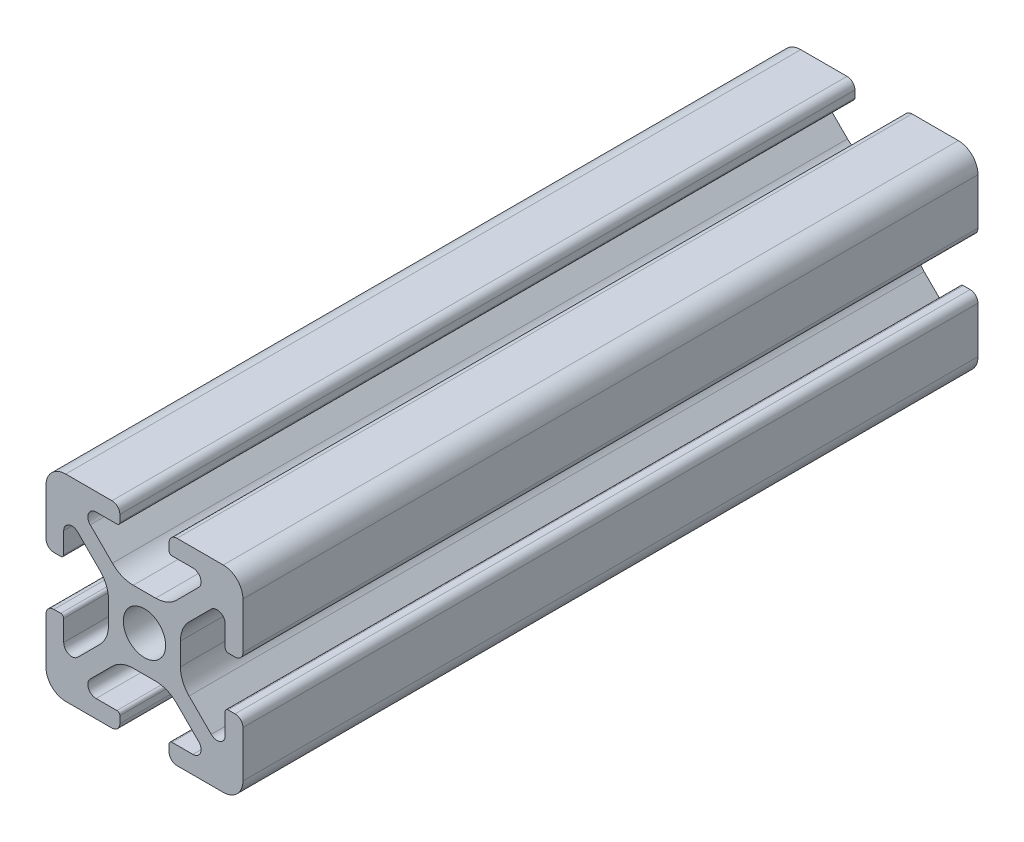
SolidWorks part; units mm, degrees
ref_plane "Front" through (0, 0, 0) normal (0, 0, 1) x (1, 0, 0)
ref_plane "Top" through (0, 0, 0) normal (0, 1, 0) x (1, 0, 0)
ref_plane "Right" through (0, 0, 0) normal (1, 0, 0) x (0, 0, -1)
sketch "Support-Front" plane through (0, 0, 0) normal (0, 0, 1) x (1, 0, 0)
  line L0 (10, 0) -> (-10, 0) construction
  line L1 (-10, -10) -> (10, -10)
  line L2 (-10, -10) -> (-10, 10)
  line L3 (-10, 10) -> (10, 10)
  line L4 (10, -10) -> (10, 10)
  line L5 (0, 10) -> (0, -10) construction
  dimension "Height-Profile" = 20
  dimension "Width-Profile" = 20
sketch "Support-Right-Length" plane through (0, 0, 0) normal (1, 0, 0) x (0, 0, -1)
  line L0 (0, -10) -> (0, 10) construction
  line L1 (-25, 10) -> (25, 10)
  line L2 (-25, 10) -> (-25, -10)
  line L3 (-25, -10) -> (25, -10)
  line L4 (25, 10) -> (25, -10)
  dimension "Length-Profile" = 50
sketch "Support-Profile" plane through (0, 0, 0) normal (0, 0, 1) x (1, 0, 0)
  line L8 (4.9176, -8.2) -> (2.8, -8.2)
  line L9 (2.5, -8.5) -> (2.5, -9.2)
  line L10 (3.3, -10) -> (8, -10)
  line L11 (10, -8) -> (10, -3.3)
  line L24 (9.2, -2.5) -> (8.5, -2.5)
  line L25 (8.2, -2.8) -> (8.2, -4.9176)
  line L26 (6.779, -5.5062) -> (4.5287, -3.2559)
  line L27 (3.65, -1.1346) -> (3.65, 1.1346)
  line L28 (4.5287, 3.2559) -> (6.779, 5.5062)
  line L29 (8.2, 4.9176) -> (8.2, 2.8)
  line L30 (8.5, 2.5) -> (9.2, 2.5)
  line L31 (10, 3.3) -> (10, 8)
  line L32 (8, 10) -> (3.3, 10)
  line L33 (2.5, 9.2) -> (2.5, 8.5)
  line L34 (2.8, 8.2) -> (4.9176, 8.2)
  line L35 (5.5062, 6.779) -> (3.2559, 4.5287)
  line L40 (1.1346, 3.65) -> (-1.1346, 3.65)
  line L41 (-3.2559, 4.5287) -> (-5.5062, 6.779)
  line L42 (-4.9176, 8.2) -> (-2.8, 8.2)
  line L43 (-2.5, 8.5) -> (-2.5, 9.2)
  line L44 (-3.3, 10) -> (-8, 10)
  line L45 (-10, 8) -> (-10, 3.3)
  line L46 (-9.2, 2.5) -> (-8.5, 2.5)
  line L47 (-8.2, 2.8) -> (-8.2, 4.9176)
  line L48 (-6.779, 5.5062) -> (-4.5287, 3.2559)
  line L49 (-3.65, 1.1346) -> (-3.65, -1.1346)
  line L50 (-4.5287, -3.2559) -> (-6.779, -5.5062)
  line L51 (-8.2, -4.9176) -> (-8.2, -2.8)
  line L52 (-8.5, -2.5) -> (-9.2, -2.5)
  line L53 (-10, -3.3) -> (-10, -8)
  line L54 (-8, -10) -> (-3.3, -10)
  line L55 (-2.5, -9.2) -> (-2.5, -8.5)
  line L56 (-2.8, -8.2) -> (-4.9176, -8.2)
  line L57 (-5.5062, -6.779) -> (-3.2559, -4.5287)
  line L58 (-1.1346, -3.65) -> (1.1346, -3.65)
  line L59 (3.2559, -4.5287) -> (5.5062, -6.779)
  circle A2 centre (0, 0) radius 2.15
  arc A3 (2.8, -8.2) -> (2.5, -8.5) centre (2.8, -8.5) ccw
  arc A5 (2.5, -9.2) -> (3.3, -10) centre (3.3, -9.2) ccw
  arc A24 (8, -10) -> (10, -8) centre (8, -8) ccw
  arc A25 (10, -3.3) -> (9.2, -2.5) centre (9.2, -3.3) ccw
  arc A26 (8.5, -2.5) -> (8.2, -2.8) centre (8.5, -2.8) ccw
  arc A27 (6.779, -5.5062) -> (8.2, -4.9176) centre (7.3676, -4.9176) ccw
  arc A28 (3.65, -1.1346) -> (4.5287, -3.2559) centre (6.65, -1.1346) ccw
  arc A29 (4.5287, 3.2559) -> (3.65, 1.1346) centre (6.65, 1.1346) ccw
  arc A30 (8.2, 4.9176) -> (6.779, 5.5062) centre (7.3676, 4.9176) ccw
  arc A31 (8.2, 2.8) -> (8.5, 2.5) centre (8.5, 2.8) ccw
  arc A32 (9.2, 2.5) -> (10, 3.3) centre (9.2, 3.3) ccw
  arc A33 (10, 8) -> (8, 10) centre (8, 8) ccw
  arc A34 (3.3, 10) -> (2.5, 9.2) centre (3.3, 9.2) ccw
  arc A35 (2.5, 8.5) -> (2.8, 8.2) centre (2.8, 8.5) ccw
  arc A38 (5.5062, 6.779) -> (4.9176, 8.2) centre (4.9176, 7.3676) ccw
  arc A39 (1.1346, 3.65) -> (3.2559, 4.5287) centre (1.1346, 6.65) ccw
  arc A44 (-3.2559, 4.5287) -> (-1.1346, 3.65) centre (-1.1346, 6.65) ccw
  arc A45 (-4.9176, 8.2) -> (-5.5062, 6.779) centre (-4.9176, 7.3676) ccw
  arc A46 (-2.8, 8.2) -> (-2.5, 8.5) centre (-2.8, 8.5) ccw
  arc A47 (-2.5, 9.2) -> (-3.3, 10) centre (-3.3, 9.2) ccw
  arc A48 (-8, 10) -> (-10, 8) centre (-8, 8) ccw
  arc A49 (-10, 3.3) -> (-9.2, 2.5) centre (-9.2, 3.3) ccw
  arc A50 (-8.5, 2.5) -> (-8.2, 2.8) centre (-8.5, 2.8) ccw
  arc A51 (-6.779, 5.5062) -> (-8.2, 4.9176) centre (-7.3676, 4.9176) ccw
  arc A52 (-3.65, 1.1346) -> (-4.5287, 3.2559) centre (-6.65, 1.1346) ccw
  arc A53 (-4.5287, -3.2559) -> (-3.65, -1.1346) centre (-6.65, -1.1346) ccw
  arc A54 (-8.2, -4.9176) -> (-6.779, -5.5062) centre (-7.3676, -4.9176) ccw
  arc A55 (-8.2, -2.8) -> (-8.5, -2.5) centre (-8.5, -2.8) ccw
  arc A56 (-9.2, -2.5) -> (-10, -3.3) centre (-9.2, -3.3) ccw
  arc A57 (-10, -8) -> (-8, -10) centre (-8, -8) ccw
  arc A58 (-3.3, -10) -> (-2.5, -9.2) centre (-3.3, -9.2) ccw
  arc A59 (-2.5, -8.5) -> (-2.8, -8.2) centre (-2.8, -8.5) ccw
  arc A60 (-5.5062, -6.779) -> (-4.9176, -8.2) centre (-4.9176, -7.3676) ccw
  arc A61 (-1.1346, -3.65) -> (-3.2559, -4.5287) centre (-1.1346, -6.65) ccw
  arc A62 (3.2559, -4.5287) -> (1.1346, -3.65) centre (1.1346, -6.65) ccw
  arc A63 (4.9176, -8.2) -> (5.5062, -6.779) centre (4.9176, -7.3676) ccw
ref_plane "Ref-Plane-1" through (0, 0, 25) normal (0, 0, 1) x (1, 0, 0)
ref_plane "Ref-Plane-2" through (0, 0, -25) normal (0, 0, 1) x (1, 0, 0)
sketch "Sketch4" plane through (0, 0, 25) normal (0, 0, 1) x (1, 0, 0)
  line L0 (-10, -10) -> (-10, 10) construction
  line L1 (-10, -10) -> (10, -10) construction
  line L2 (10, -10) -> (10, 10) construction
  line L3 (-10, 10) -> (10, 10) construction
  line L4 (-10, -10) -> (-10, 10)
  line L5 (-10, -10) -> (10, -10)
  line L6 (10, -10) -> (10, 10)
  line L7 (-10, 10) -> (10, 10)
extrude "Body" add sketch "Sketch4" against normal blind 74.65
sketch "Sketch16" plane through (0, 0, 0) normal (0, 0, 1) x (1, 0, 0)
  line L40 (4.9176, -8.2) -> (2.8, -8.2)
  line L41 (2.5, -8.5) -> (2.5, -9.2)
  line L42 (3.3, -10) -> (8, -10)
  line L43 (10, -8) -> (10, -3.3)
  line L44 (9.2, -2.5) -> (8.5, -2.5)
  line L45 (8.2, -2.8) -> (8.2, -4.9176)
  line L46 (6.779, -5.5062) -> (4.5287, -3.2559)
  line L47 (3.65, -1.1346) -> (3.65, 1.1346)
  line L48 (4.5287, 3.2559) -> (6.779, 5.5062)
  line L49 (8.2, 4.9176) -> (8.2, 2.8)
  line L50 (8.5, 2.5) -> (9.2, 2.5)
  line L51 (10, 3.3) -> (10, 8)
  line L52 (8, 10) -> (3.3, 10)
  line L53 (2.5, 9.2) -> (2.5, 8.5)
  line L54 (2.8, 8.2) -> (4.9176, 8.2)
  line L55 (5.5062, 6.779) -> (3.2559, 4.5287)
  line L56 (1.1346, 3.65) -> (-1.1346, 3.65)
  line L57 (-3.2559, 4.5287) -> (-5.5062, 6.779)
  line L58 (-4.9176, 8.2) -> (-2.8, 8.2)
  line L59 (-2.5, 8.5) -> (-2.5, 9.2)
  line L60 (-3.3, 10) -> (-8, 10)
  line L61 (-10, 8) -> (-10, 3.3)
  line L62 (-9.2, 2.5) -> (-8.5, 2.5)
  line L63 (-8.2, 2.8) -> (-8.2, 4.9176)
  line L64 (-6.779, 5.5062) -> (-4.5287, 3.2559)
  line L65 (-3.65, 1.1346) -> (-3.65, -1.1346)
  line L66 (-4.5287, -3.2559) -> (-6.779, -5.5062)
  line L67 (-8.2, -4.9176) -> (-8.2, -2.8)
  line L68 (-8.5, -2.5) -> (-9.2, -2.5)
  line L69 (-10, -3.3) -> (-10, -8)
  line L70 (-8, -10) -> (-3.3, -10)
  line L71 (-2.5, -9.2) -> (-2.5, -8.5)
  line L72 (-2.8, -8.2) -> (-4.9176, -8.2)
  line L73 (-5.5062, -6.779) -> (-3.2559, -4.5287)
  line L74 (-1.1346, -3.65) -> (1.1346, -3.65)
  line L75 (3.2559, -4.5287) -> (5.5062, -6.779)
  line L76 (4.9176, -8.2) -> (2.8, -8.2)
  line L77 (2.5, -8.5) -> (2.5, -9.2)
  line L78 (3.3, -10) -> (8, -10)
  line L79 (10, -8) -> (10, -3.3)
  line L80 (9.2, -2.5) -> (8.5, -2.5)
  line L81 (8.2, -2.8) -> (8.2, -4.9176)
  line L82 (6.779, -5.5062) -> (4.5287, -3.2559)
  line L83 (3.65, -1.1346) -> (3.65, 1.1346)
  line L84 (4.5287, 3.2559) -> (6.779, 5.5062)
  line L85 (8.2, 4.9176) -> (8.2, 2.8)
  line L86 (8.5, 2.5) -> (9.2, 2.5)
  line L87 (10, 3.3) -> (10, 8)
  line L88 (8, 10) -> (3.3, 10)
  line L89 (2.5, 9.2) -> (2.5, 8.5)
  line L90 (2.8, 8.2) -> (4.9176, 8.2)
  line L91 (5.5062, 6.779) -> (3.2559, 4.5287)
  line L92 (1.1346, 3.65) -> (-1.1346, 3.65)
  line L93 (-3.2559, 4.5287) -> (-5.5062, 6.779)
  line L94 (-4.9176, 8.2) -> (-2.8, 8.2)
  line L95 (-2.5, 8.5) -> (-2.5, 9.2)
  line L96 (-3.3, 10) -> (-8, 10)
  line L97 (-10, 8) -> (-10, 3.3)
  line L98 (-9.2, 2.5) -> (-8.5, 2.5)
  line L99 (-8.2, 2.8) -> (-8.2, 4.9176)
  line L100 (-6.779, 5.5062) -> (-4.5287, 3.2559)
  line L101 (-3.65, 1.1346) -> (-3.65, -1.1346)
  line L102 (-4.5287, -3.2559) -> (-6.779, -5.5062)
  line L103 (-8.2, -4.9176) -> (-8.2, -2.8)
  line L104 (-8.5, -2.5) -> (-9.2, -2.5)
  line L105 (-10, -3.3) -> (-10, -8)
  line L106 (-8, -10) -> (-3.3, -10)
  line L107 (-2.5, -9.2) -> (-2.5, -8.5)
  line L108 (-2.8, -8.2) -> (-4.9176, -8.2)
  line L109 (-5.5062, -6.779) -> (-3.2559, -4.5287)
  line L110 (-1.1346, -3.65) -> (1.1346, -3.65)
  line L111 (3.2559, -4.5287) -> (5.5062, -6.779)
  circle A7 centre (0, 0) radius 2.15 construction
  circle A8 centre (0, 0) radius 2.15
  arc A43 (2.8, -8.2) -> (2.5, -8.5) centre (2.8, -8.5) ccw
  arc A44 (2.5, -9.2) -> (3.3, -10) centre (3.3, -9.2) ccw
  arc A45 (8, -10) -> (10, -8) centre (8, -8) ccw
  arc A46 (10, -3.3) -> (9.2, -2.5) centre (9.2, -3.3) ccw
  arc A47 (8.5, -2.5) -> (8.2, -2.8) centre (8.5, -2.8) ccw
  arc A48 (6.779, -5.5062) -> (8.2, -4.9176) centre (7.3676, -4.9176) ccw
  arc A49 (3.65, -1.1346) -> (4.5287, -3.2559) centre (6.65, -1.1346) ccw
  arc A50 (4.5287, 3.2559) -> (3.65, 1.1346) centre (6.65, 1.1346) ccw
  arc A51 (8.2, 4.9176) -> (6.779, 5.5062) centre (7.3676, 4.9176) ccw
  arc A52 (8.2, 2.8) -> (8.5, 2.5) centre (8.5, 2.8) ccw
  arc A53 (9.2, 2.5) -> (10, 3.3) centre (9.2, 3.3) ccw
  arc A54 (10, 8) -> (8, 10) centre (8, 8) ccw
  arc A55 (3.3, 10) -> (2.5, 9.2) centre (3.3, 9.2) ccw
  arc A56 (2.5, 8.5) -> (2.8, 8.2) centre (2.8, 8.5) ccw
  arc A57 (5.5062, 6.779) -> (4.9176, 8.2) centre (4.9176, 7.3676) ccw
  arc A58 (1.1346, 3.65) -> (3.2559, 4.5287) centre (1.1346, 6.65) ccw
  arc A59 (-3.2559, 4.5287) -> (-1.1346, 3.65) centre (-1.1346, 6.65) ccw
  arc A60 (-4.9176, 8.2) -> (-5.5062, 6.779) centre (-4.9176, 7.3676) ccw
  arc A61 (-2.8, 8.2) -> (-2.5, 8.5) centre (-2.8, 8.5) ccw
  arc A62 (-2.5, 9.2) -> (-3.3, 10) centre (-3.3, 9.2) ccw
  arc A63 (-8, 10) -> (-10, 8) centre (-8, 8) ccw
  arc A64 (-10, 3.3) -> (-9.2, 2.5) centre (-9.2, 3.3) ccw
  arc A65 (-8.5, 2.5) -> (-8.2, 2.8) centre (-8.5, 2.8) ccw
  arc A66 (-6.779, 5.5062) -> (-8.2, 4.9176) centre (-7.3676, 4.9176) ccw
  arc A67 (-3.65, 1.1346) -> (-4.5287, 3.2559) centre (-6.65, 1.1346) ccw
  arc A68 (-4.5287, -3.2559) -> (-3.65, -1.1346) centre (-6.65, -1.1346) ccw
  arc A69 (-8.2, -4.9176) -> (-6.779, -5.5062) centre (-7.3676, -4.9176) ccw
  arc A70 (-8.2, -2.8) -> (-8.5, -2.5) centre (-8.5, -2.8) ccw
  arc A71 (-9.2, -2.5) -> (-10, -3.3) centre (-9.2, -3.3) ccw
  arc A72 (-10, -8) -> (-8, -10) centre (-8, -8) ccw
  arc A73 (-3.3, -10) -> (-2.5, -9.2) centre (-3.3, -9.2) ccw
  arc A74 (-2.5, -8.5) -> (-2.8, -8.2) centre (-2.8, -8.5) ccw
  arc A75 (-5.5062, -6.779) -> (-4.9176, -8.2) centre (-4.9176, -7.3676) ccw
  arc A76 (-1.1346, -3.65) -> (-3.2559, -4.5287) centre (-1.1346, -6.65) ccw
  arc A77 (3.2559, -4.5287) -> (1.1346, -3.65) centre (1.1346, -6.65) ccw
  arc A78 (4.9176, -8.2) -> (5.5062, -6.779) centre (4.9176, -7.3676) ccw
  arc A79 (2.8, -8.2) -> (2.5, -8.5) centre (2.8, -8.5) ccw
  arc A80 (2.5, -9.2) -> (3.3, -10) centre (3.3, -9.2) ccw
  arc A81 (8, -10) -> (10, -8) centre (8, -8) ccw
  arc A82 (10, -3.3) -> (9.2, -2.5) centre (9.2, -3.3) ccw
  arc A83 (8.5, -2.5) -> (8.2, -2.8) centre (8.5, -2.8) ccw
  arc A84 (6.779, -5.5062) -> (8.2, -4.9176) centre (7.3676, -4.9176) ccw
  arc A85 (3.65, -1.1346) -> (4.5287, -3.2559) centre (6.65, -1.1346) ccw
  arc A86 (4.5287, 3.2559) -> (3.65, 1.1346) centre (6.65, 1.1346) ccw
  arc A87 (8.2, 4.9176) -> (6.779, 5.5062) centre (7.3676, 4.9176) ccw
  arc A88 (8.2, 2.8) -> (8.5, 2.5) centre (8.5, 2.8) ccw
  arc A89 (9.2, 2.5) -> (10, 3.3) centre (9.2, 3.3) ccw
  arc A90 (10, 8) -> (8, 10) centre (8, 8) ccw
  arc A91 (3.3, 10) -> (2.5, 9.2) centre (3.3, 9.2) ccw
  arc A92 (2.5, 8.5) -> (2.8, 8.2) centre (2.8, 8.5) ccw
  arc A93 (5.5062, 6.779) -> (4.9176, 8.2) centre (4.9176, 7.3676) ccw
  arc A94 (1.1346, 3.65) -> (3.2559, 4.5287) centre (1.1346, 6.65) ccw
  arc A95 (-3.2559, 4.5287) -> (-1.1346, 3.65) centre (-1.1346, 6.65) ccw
  arc A96 (-4.9176, 8.2) -> (-5.5062, 6.779) centre (-4.9176, 7.3676) ccw
  arc A97 (-2.8, 8.2) -> (-2.5, 8.5) centre (-2.8, 8.5) ccw
  arc A98 (-2.5, 9.2) -> (-3.3, 10) centre (-3.3, 9.2) ccw
  arc A99 (-8, 10) -> (-10, 8) centre (-8, 8) ccw
  arc A100 (-10, 3.3) -> (-9.2, 2.5) centre (-9.2, 3.3) ccw
  arc A101 (-8.5, 2.5) -> (-8.2, 2.8) centre (-8.5, 2.8) ccw
  arc A102 (-6.779, 5.5062) -> (-8.2, 4.9176) centre (-7.3676, 4.9176) ccw
  arc A103 (-3.65, 1.1346) -> (-4.5287, 3.2559) centre (-6.65, 1.1346) ccw
  arc A104 (-4.5287, -3.2559) -> (-3.65, -1.1346) centre (-6.65, -1.1346) ccw
  arc A105 (-8.2, -4.9176) -> (-6.779, -5.5062) centre (-7.3676, -4.9176) ccw
  arc A106 (-8.2, -2.8) -> (-8.5, -2.5) centre (-8.5, -2.8) ccw
  arc A107 (-9.2, -2.5) -> (-10, -3.3) centre (-9.2, -3.3) ccw
  arc A108 (-10, -8) -> (-8, -10) centre (-8, -8) ccw
  arc A109 (-3.3, -10) -> (-2.5, -9.2) centre (-3.3, -9.2) ccw
  arc A110 (-2.5, -8.5) -> (-2.8, -8.2) centre (-2.8, -8.5) ccw
  arc A111 (-5.5062, -6.779) -> (-4.9176, -8.2) centre (-4.9176, -7.3676) ccw
  arc A112 (-1.1346, -3.65) -> (-3.2559, -4.5287) centre (-1.1346, -6.65) ccw
  arc A113 (3.2559, -4.5287) -> (1.1346, -3.65) centre (1.1346, -6.65) ccw
  arc A114 (4.9176, -8.2) -> (5.5062, -6.779) centre (4.9176, -7.3676) ccw
  dimension "D1" = 0
extrude "Cut-Profile" cut sketch "Sketch16" against normal through all and the other way through all flip side to cut
